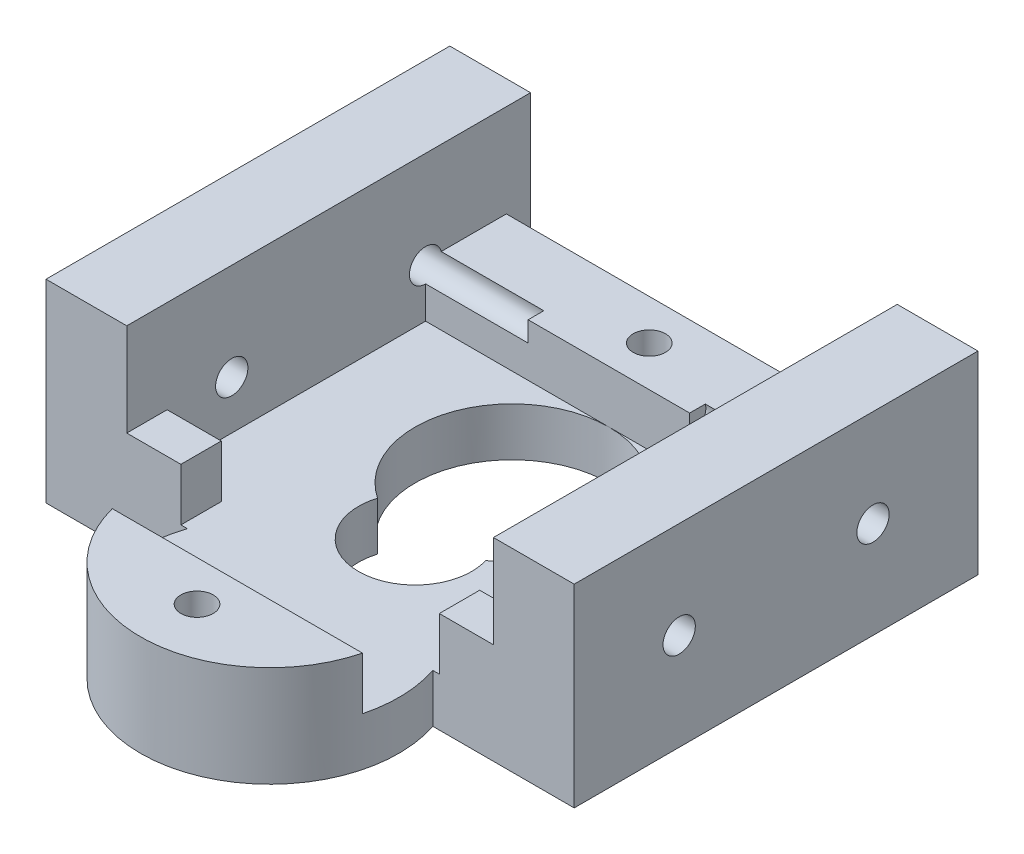
SolidWorks part; units mm, degrees
ref_plane "Alzado" through (0, 0, 0) normal (0, 0, 1) x (1, 0, 0)
ref_plane "Planta" through (0, 0, 0) normal (0, 1, 0) x (1, 0, 0)
ref_plane "Vista lateral" through (0, 0, 0) normal (1, 0, 0) x (0, 0, -1)
sketch "Croquis1" plane through (0, 0, 0) normal (0, 1, 0) x (1, 0, 0)
  line L0 (7.8263, -7.1365) -> (16.5769, -7.1365)
  line L1 (-16.1231, 17.8635) -> (16.5769, 17.8635)
  line L2 (-16.1231, 17.8635) -> (-16.1231, -7.1365)
  line L3 (-16.1231, -7.1365) -> (-7.3724, -7.1365)
  line L4 (16.5769, 17.8635) -> (16.5769, -7.1365)
  arc A0 (-7.3724, -7.1365) -> (7.8263, -7.1365) centre (0.2269, -9.6365) ccw
  arc A1 (-3.1204, 0.386) -> (3.5736, 0.388) centre (0.2269, -0.6365) ccw
  arc A2 (3.5736, 0.388) -> (-3.1204, 0.386) centre (0.2252, 5.3646) ccw
  circle A3 centre (0.2269, 13.8635) radius 1
  circle A4 centre (0.2269, -14.1365) radius 1
extrude "Saliente-Extruir1" add sketch "Croquis1" along normal blind 3
sketch "Croquis2" plane through (0, 3, 0) normal (0, 1, 0) x (1, 0, 0)
  line L0 (-7.5191, -11.6365) -> (7.9729, -11.6365)
  line L2 (-16.1231, 17.8635) -> (-11.1231, 17.8635)
  line L3 (-16.1231, 17.8635) -> (-16.1231, -7.1365)
  line L5 (-11.1231, 17.8635) -> (-11.1231, 16.3635)
  line L6 (16.5769, 17.8635) -> (-16.1231, 17.8635) construction
  line L8 (16.5769, -7.1365) -> (16.5769, 17.8635)
  line L9 (16.5769, 17.8635) -> (11.5769, 17.8635)
  line L10 (11.5769, -4.6365) -> (11.5769, 11.3628)
  line L11 (-16.1231, -7.1365) -> (-7.7731, -7.1365)
  line L12 (-11.1231, 16.3635) -> (11.5769, 16.3635)
  line L14 (-11.1231, 11.3628) -> (11.5769, 11.3628)
  line L18 (-11.1231, -4.6365) -> (-7.7731, -4.6365)
  line L19 (-7.7731, -7.1365) -> (-7.7731, -4.6365)
  line L22 (11.5769, -4.6365) -> (8.2269, -4.6365)
  line L23 (8.2269, -7.1365) -> (8.2269, -4.6365)
  line L24 (8.2269, -7.1365) -> (16.5769, -7.1365)
  line L25 (-11.1231, 11.3628) -> (-11.1231, -4.6365)
  line L26 (11.5769, 16.3635) -> (11.5769, 17.8635)
  arc A0 (-7.5191, -11.6365) -> (7.9729, -11.6365) centre (0.2269, -9.6365) ccw
  arc A1 (3.5736, 0.388) -> (-3.1204, 0.386) centre (0.2252, 5.3646) ccw construction
  dimension "D1" = 2
  dimension "D2" = 22.7
  dimension "D3" = 3.35
  dimension "D4" = 1.5
  dimension "D5" = 2.5
extrude "Saliente-Extruir2" add sketch "Croquis2" along normal blind 3.25
sketch "Croquis3" plane through (0, 6.25, 0) normal (0, 1, 0) x (1, 0, 0)
  line L1 (-16.1231, -7.1365) -> (-11.1231, -7.1365)
  line L2 (-16.1231, -7.1365) -> (-16.1231, 17.8635)
  line L3 (-16.1231, 17.8635) -> (-11.1231, 17.8635)
  line L4 (-11.1231, -7.1365) -> (-11.1231, 17.8635)
  line L5 (11.5769, 17.8635) -> (16.5769, 17.8635)
  line L6 (11.5769, 17.8635) -> (11.5769, -7.1365)
  line L7 (11.5769, -7.1365) -> (16.5769, -7.1365)
  line L8 (16.5769, 17.8635) -> (16.5769, -7.1365)
extrude "Saliente-Extruir3" add sketch "Croquis3" along normal blind 5.75
sketch "Croquis4" plane through (-16.1231, 0, 0) normal (-1, 0, 0) x (0, 0, 1)
  line L0 (-17.8635, 12) -> (-17.8635, 0) construction
  line L1 (-17.8635, 0) -> (7.1365, 0) construction
  circle A0 centre (-11.3635, 6) radius 1
  circle A1 centre (0.6365, 6) radius 1
  dimension "D2" = 2
  dimension "D1" = 6.5
  dimension "D3" = 12
  dimension "D4" = 6
extrude "Cortar-Extruir1" cut sketch "Croquis4" against normal blind 11.35
sketch "Croquis5" plane through (16.5769, 0, 0) normal (1, 0, 0) x (0, 0, -1)
  line L0 (17.8635, 12) -> (17.8635, 0) construction
  line L1 (-7.1365, 0) -> (17.8635, 0) construction
  circle A0 centre (11.3635, 6) radius 1
  circle A1 centre (-0.6365, 6) radius 1
  dimension "D4" = 2
  dimension "D1" = 12
  dimension "D2" = 6.5
  dimension "D3" = 6
extrude "Cortar-Extruir2" cut sketch "Croquis5" against normal blind 11.35
sketch "Croquis6" plane through (0, 0, 0) normal (0, -1, 0) x (1, 0, 0)
  circle A0 centre (0.2269, -13.8635) radius 1 construction
  circle A1 centre (0.2269, 14.1365) radius 1 construction
  circle A2 centre (0.2269, -13.8635) radius 1
  circle A3 centre (0.2269, 14.1365) radius 1
extrude "Cortar-Extruir3" cut sketch "Croquis6" against normal blind 11.35
